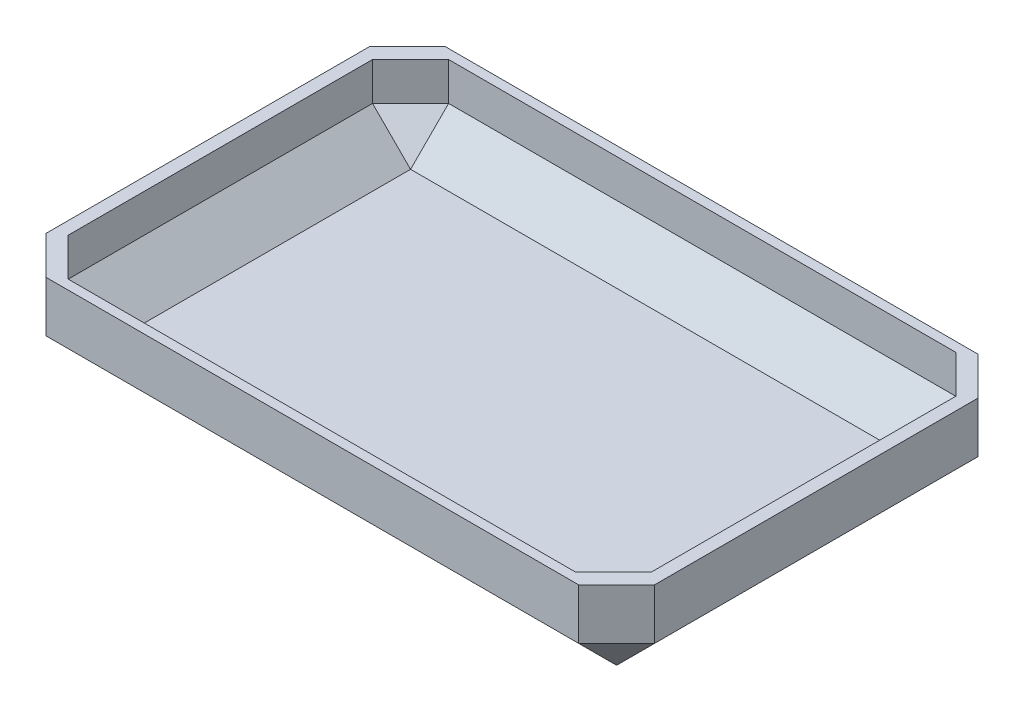
SolidWorks part; units mm, degrees
ref_plane "Front Plane" through (0, 0, 0) normal (0, 0, 1) x (1, 0, 0)
ref_plane "Top Plane" through (0, 0, 0) normal (0, 1, 0) x (1, 0, 0)
ref_plane "Right Plane" through (0, 0, 0) normal (1, 0, 0) x (0, 0, -1)
sketch "Sketch1" plane through (0, 0, 0) normal (0, 1, 0) x (1, 0, 0)
  line L1 (240, 157.5) -> (-240, 157.5)
  line L2 (240, 157.5) -> (240, -157.5)
  line L3 (240, -157.5) -> (-240, -157.5)
  line L4 (-240, 157.5) -> (-240, -157.5)
  line L5 (240, 157.5) -> (-240, -157.5) construction
  line L6 (240, -157.5) -> (-240, 157.5) construction
  point P0 (0, 0)
  dimension "D1" = 315
  dimension "D2" = 480
extrude "Boss-Extrude1" add sketch "Sketch1" along normal blind 70
sketch "Sketch3" plane through (0, 70, 0) normal (0, 1, 0) x (1, 0, 0)
  line L1 (-230, 150) -> (230, 150)
  line L2 (-230, 150) -> (-230, -150)
  line L3 (-230, -150) -> (230, -150)
  line L4 (230, 150) -> (230, -150)
  line L5 (-230, 150) -> (230, -150) construction
  line L6 (-230, -150) -> (230, 150) construction
  point P0 (0, 0)
  dimension "D1" = 300
  dimension "D2" = 460
extrude "Cut-Extrude1" cut sketch "Sketch3" against normal blind 60
chamfer "Chamfer1" distance 30 angle 45 16 edges at (230, 40, -150) (-230, 40, 150) (230, 40, 150) (-230, 40, -150) (-230, 10, 0) (0, 10, -150) (230, 10, 0) (0, 10, 150) (-240, 35, 157.5) (240, 35, 157.5) (-240, 35, -157.5) (-240, 0, 0) (0, 0, 157.5) (0, 0, -157.5) (240, 0, 0) (240, 35, -157.5)
